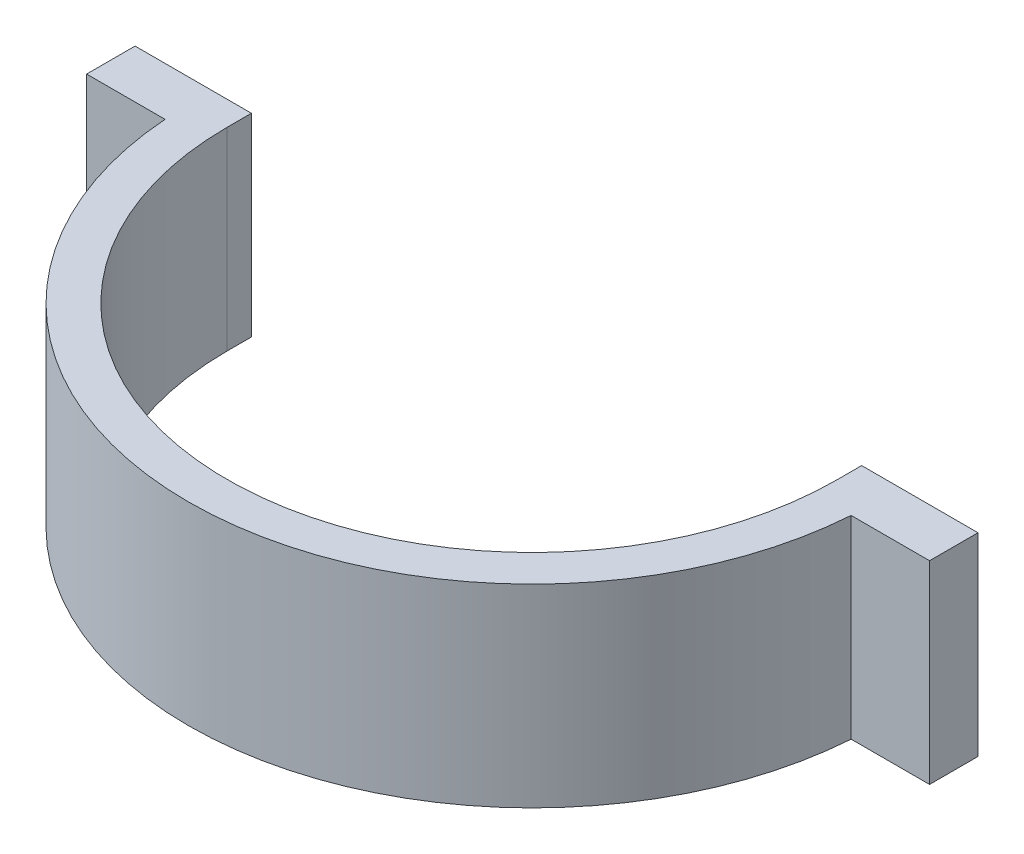
SolidWorks part; units mm, degrees
material "ABS"
ref_plane "Front Plane" through (0, 0, 0) normal (0, 0, 1) x (1, 0, 0)
ref_plane "Top Plane" through (0, 0, 0) normal (0, 1, 0) x (1, 0, 0)
ref_plane "Right Plane" through (0, 0, 0) normal (1, 0, 0) x (0, 0, -1)
sketch "Sketch2" plane through (0, 0, 0) normal (0, 1, 0) x (1, 0, 0)
  circle A0 centre (0, 0) radius 39.9923
  circle A1 centre (0, 0) radius 45.0723
extrude "Boss-Extrude1" add sketch "Sketch2" along normal blind 25.4
sketch "Sketch3" plane through (0, 0, 0) normal (0, 0, 1) x (1, 0, 0)
  line L1 (-45.0723, 25.4) -> (45.0723, 25.4)
  line L2 (-45.0723, 25.4) -> (-45.0723, 0)
  line L3 (-45.0723, 0) -> (45.0723, 0)
  line L4 (45.0723, 25.4) -> (45.0723, 0)
extrude "Cut-Extrude1" cut sketch "Sketch3" against normal through all
sketch "Sketch5" plane through (0, 0, 0) normal (0, 0, -1) x (-1, 0, 0)
  line L0 (0, 0) -> (0, 39.1373) construction
  line L1 (-45.0814, 25.4) -> (-39.9923, 25.4)
  line L2 (-45.1672, 0) -> (-39.9923, 0)
  line L3 (-39.9923, 25.4) -> (-39.9923, 0)
  line L4 (-45.0814, 25.4) -> (-55.2414, 25.4)
  line L5 (-55.2414, 25.4) -> (-55.2414, 0)
  line L6 (-55.2414, 0) -> (-45.1672, 0)
  line L14 (-39.9923, 0) -> (-39.9923, 25.4) construction
  line L15 (-39.9923, 0) -> (-45.0723, 0) construction
  line L16 (45.0814, 25.4) -> (55.2414, 25.4)
  line L17 (55.2414, 25.4) -> (55.2414, 0)
  line L18 (55.2414, 0) -> (45.1672, 0)
  line L19 (45.1672, 0) -> (39.9923, 0)
  line L20 (39.9923, 25.4) -> (39.9923, 0)
  line L21 (45.0814, 25.4) -> (39.9923, 25.4)
  point P6 (0, 0)
extrude "Boss-Extrude2" add sketch "Sketch5" along normal mid plane 6.35
